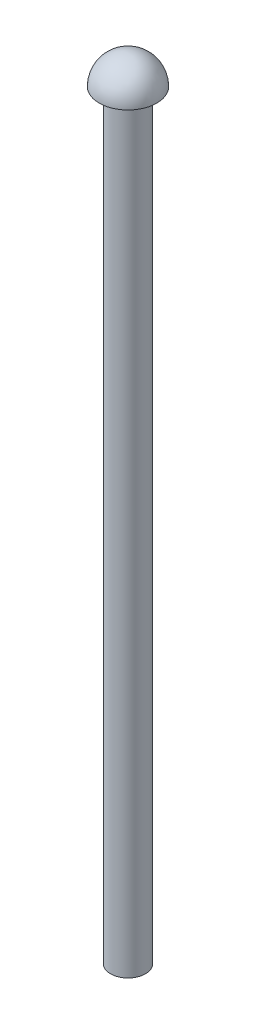
SolidWorks part; units mm, degrees
ref_plane "Front Plane" through (0, 0, 0) normal (0, 0, 1) x (1, 0, 0)
ref_plane "Top Plane" through (0, 0, 0) normal (0, 1, 0) x (1, 0, 0)
ref_plane "Right Plane" through (0, 0, 0) normal (1, 0, 0) x (0, 0, -1)
ref_axis "Axis1" through (0, -0.072, 0) along (0, 1, 0)
sketch "Sketch1" plane through (0, 0, 0) normal (1, 0, 0) x (0, 0, -1)
  line L0 (0, 0.792) -> (0, -0.792) construction
  line L1 (0, 0) -> (1.44, 0)
  arc A0 (0, 1.44) -> (1.44, 0) centre (0, 0) cw
revolve "Revolve-Thin4" add sketch "Sketch1" angle 360 about axis through (0, -0.072, 0) along (0, 1, 0) wall 0.1
sketch "Sketch4" plane through (0, 0, 0) normal (0, -1, 0) x (1, 0, 0)
  circle A0 centre (0, 0) radius 0.875
extrude "Boss-Extrude1" add sketch "Sketch4" along normal blind 38
